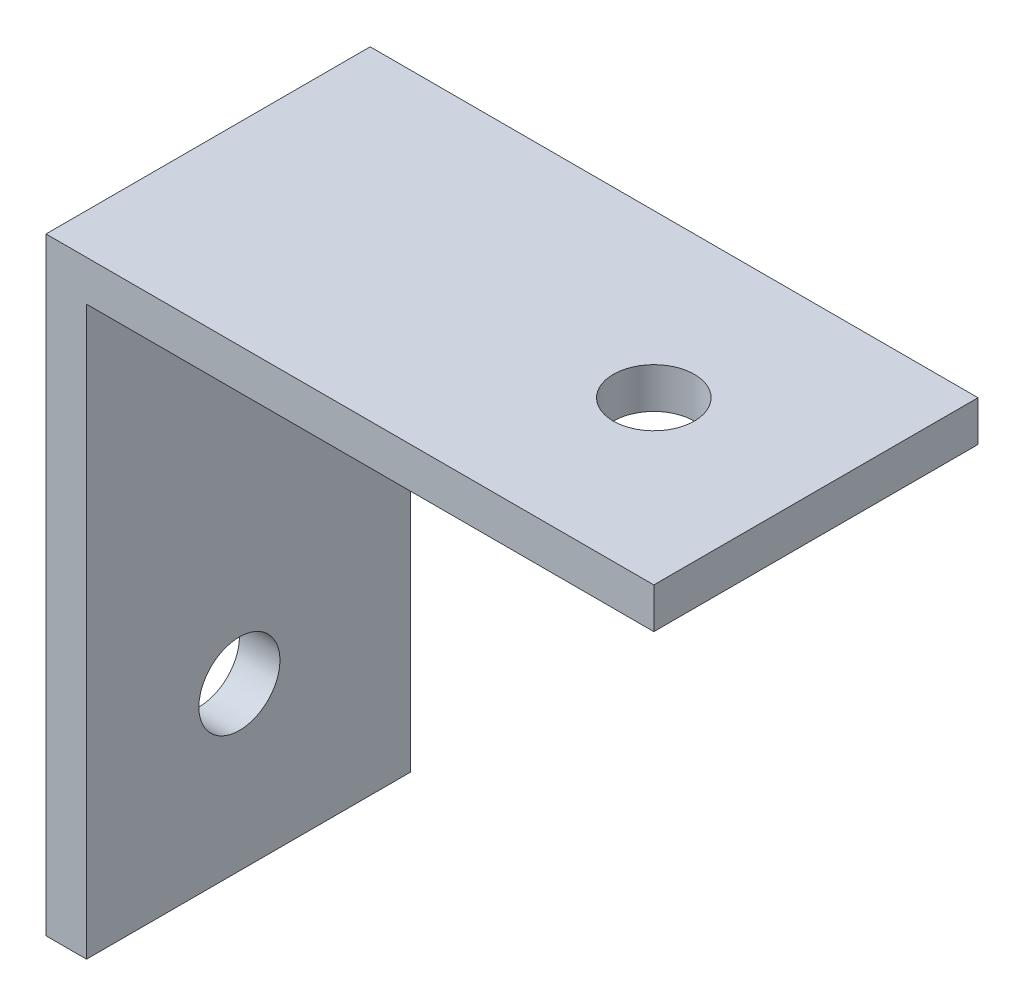
SolidWorks part; units mm, degrees
ref_plane "前视基准面" through (0, 0, 0) normal (0, 0, 1) x (1, 0, 0)
ref_plane "上视基准面" through (0, 0, 0) normal (0, 1, 0) x (1, 0, 0)
ref_plane "右视基准面" through (0, 0, 0) normal (1, 0, 0) x (0, 0, -1)
sketch "草图1" plane through (0, 0, 0) normal (0, 0, 1) x (1, 0, 0)
  line L0 (-27.2817, 17.8141) -> (-27.2817, -12.1859)
  line L1 (-27.2817, -12.1859) -> (-25.2817, -12.1859)
  line L2 (-25.2817, -12.1859) -> (-25.2817, 15.8141)
  line L3 (-25.2817, 15.8141) -> (2.7183, 15.8141)
  line L4 (2.7183, 15.8141) -> (2.7183, 17.8141)
  line L5 (2.7183, 17.8141) -> (-27.2817, 17.8141)
  dimension "D1" = 30
  dimension "D2" = 2
  dimension "D3" = 28
  dimension "D4" = 28
extrude "凸台-拉伸1" add sketch "草图1" along normal blind 16
sketch "草图2" plane through (0, 17.8141, 0) normal (0, 1, 0) x (1, 0, 0)
  line L0 (-27.2817, -8) -> (-5.2817, -8) construction
  line L1 (-27.2817, -16) -> (-27.2817, 0) construction
  circle A0 centre (-5.2817, -8) radius 2
  dimension "D2" = 4
  dimension "D1" = 22
extrude "切除-拉伸1" cut sketch "草图2" against normal blind 16
sketch "草图3" plane through (-27.2817, 0, 0) normal (-1, 0, 0) x (0, 0, 1)
  line L0 (8, 17.8141) -> (8.4544, -4.1812) construction
  line L1 (16, 17.8141) -> (0, 17.8141) construction
  circle A0 centre (8.4544, -4.1812) radius 2
  dimension "D2" = 4
  dimension "D1" = 22
extrude "切除-拉伸2" cut sketch "草图3" against normal blind 16
